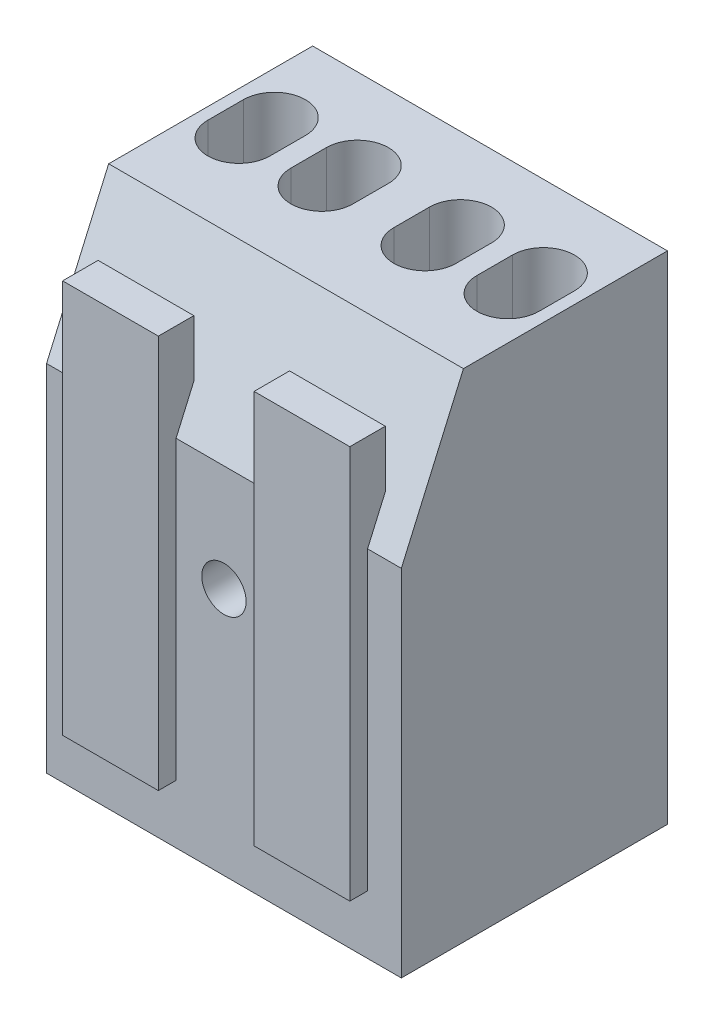
SolidWorks part; units mm, degrees
ref_plane "Front Plane" through (0, 0, 0) normal (0, 0, 1) x (1, 0, 0)
ref_plane "Top Plane" through (0, 0, 0) normal (0, 1, 0) x (1, 0, 0)
ref_plane "Right Plane" through (0, 0, 0) normal (1, 0, 0) x (0, 0, -1)
sketch "Sketch1" plane through (0, 0, 0) normal (0, 0, 1) x (1, 0, 0)
  line L0 (-10, 14) -> (10, -14) construction
  line L1 (-10, 14) -> (10, 14)
  line L2 (-10, 14) -> (-10, -14)
  line L3 (-10, -14) -> (10, -14)
  line L4 (10, 14) -> (10, -14)
  dimension "D1" = 28
  dimension "D2" = 20
extrude "Boss-Extrude1" add sketch "Sketch1" along normal blind 15
sketch "Sketch2" plane through (10, 0, 0) normal (1, 0, 0) x (0, 0, -1)
  line L0 (-11.5, 14) -> (-15, 14)
  line L1 (-15, 14) -> (0, 14) construction
  line L2 (-15, 14) -> (-15, 6)
  line L3 (-15, -14) -> (-15, 14) construction
  line L4 (-15, 6) -> (-11.5, 14)
  dimension "D1" = 3.5
  dimension "D2" = 8
extrude "Cut-Extrude1" cut sketch "Sketch2" against normal through all
sketch "Sketch3" plane through (0, 14, 0) normal (0, 1, 0) x (1, 0, 0)
  line L0 (2.9045, -4.5728) -> (2.9045, -6.5728) construction
  line L1 (4.6545, -4.5728) -> (4.6545, -6.5728)
  line L2 (1.1545, -4.5728) -> (1.1545, -6.5728)
  line L3 (7.5836, -4.5728) -> (7.5836, -6.5728) construction
  line L4 (9.3336, -4.5728) -> (9.3336, -6.5728)
  line L5 (5.8336, -4.5728) -> (5.8336, -6.5728)
  arc A0 (4.6545, -4.5728) -> (1.1545, -4.5728) centre (2.9045, -4.5728) ccw
  arc A1 (1.1545, -6.5728) -> (4.6545, -6.5728) centre (2.9045, -6.5728) ccw
  arc A2 (9.3336, -4.5728) -> (5.8336, -4.5728) centre (7.5836, -4.5728) ccw
  arc A3 (5.8336, -6.5728) -> (9.3336, -6.5728) centre (7.5836, -6.5728) ccw
  point P2 (2.9045, -5.5728)
  point P7 (7.5836, -5.5728)
  dimension "D1" = 2
  dimension "D2" = 3.5
extrude "Cut-Extrude2" cut sketch "Sketch3" against normal blind 5
sketch "Sketch4" plane through (0, 0, 15) normal (0, 0, 1) x (1, 0, 0)
  line L1 (2.6985, 11.4874) -> (8.0955, 11.4874)
  line L2 (2.6985, 11.4874) -> (2.6985, -10.7003)
  line L3 (2.6985, -10.7003) -> (8.0955, -10.7003)
  line L4 (8.0955, 11.4874) -> (8.0955, -10.7003)
extrude "Boss-Extrude2" add sketch "Sketch4" along normal mid plane 2
mirror "Mirror1" about plane through (0, 0, 0) normal (1, 0, 0) of "Boss-Extrude2", "Cut-Extrude2"
sketch "Sketch5" plane through (0, 0, 15) normal (0, 0, 1) x (1, 0, 0)
  circle A0 centre (0, 0) radius 1.25
  dimension "D1" = 2.5
extrude "Cut-Extrude3" cut sketch "Sketch5" against normal through all
